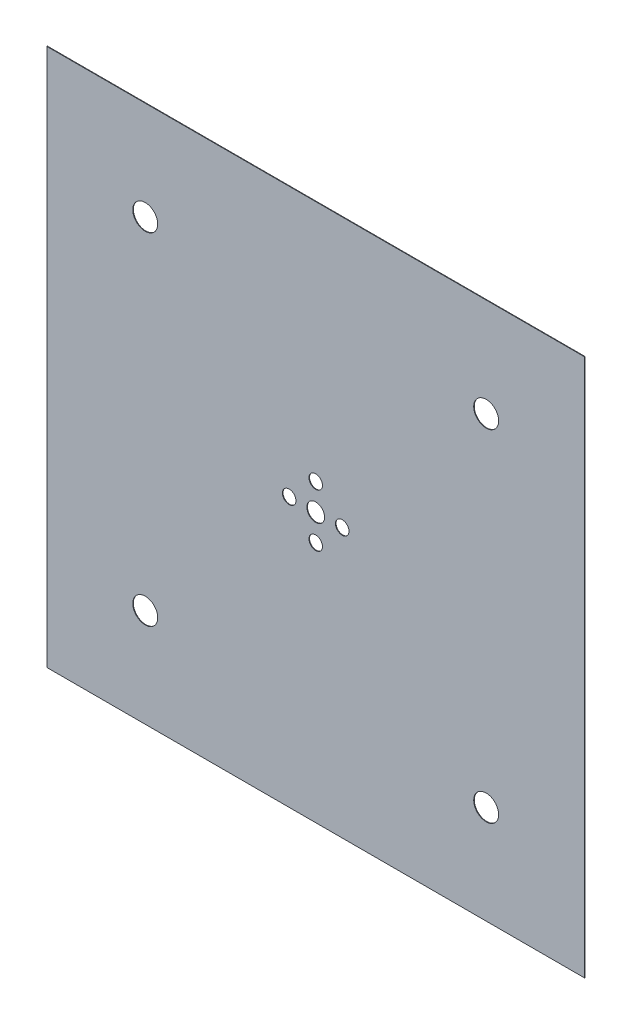
SolidWorks part; units mm, degrees
ref_plane "Front" through (0, 0, 0) normal (0, 0, 1) x (1, 0, 0)
ref_plane "Top" through (0, 0, 0) normal (0, 1, 0) x (1, 0, 0)
ref_plane "Right" through (0, 0, 0) normal (1, 0, 0) x (0, 0, -1)
sketch "Sketch1" plane through (0, 0, 0) normal (0, 0, 1) x (1, 0, 0)
  line L0 (0, 1420) -> (0, -1420) construction
  line L1 (-1420, 1420) -> (1420, 1420)
  line L2 (-1420, 1420) -> (-1420, -1420)
  line L3 (-1420, -1420) -> (1420, -1420)
  line L4 (1420, 1420) -> (1420, -1420)
  line L5 (-1420, 1420) -> (1420, -1420) construction
  line L6 (-1420, -1420) -> (1420, 1420) construction
  line L7 (-1420, 0) -> (1420, 0) construction
  circle A0 centre (0, 0) radius 46.75
  circle A1 centre (0, 140) radius 35.6375
  circle A2 centre (-900, 900) radius 65.8
  circle A3 centre (900, -900) radius 65.8
  circle A4 centre (0, -140) radius 35.6375
  circle A5 centre (900, 900) radius 65.8
  circle A6 centre (-900, -900) radius 65.8
  circle A7 centre (140, 0) radius 35.6375
  circle A8 centre (-140, 0) radius 35.6375
  point P0 (0, 0)
  dimension "D3" = 93.5
  dimension "D4" = 71.275
  dimension "D6" = 131.6
  dimension "D1" = 2840
  dimension "D2" = 2840
  dimension "D5" = 140
  dimension "D7" = 900
extrude "Boss-Extrude1" add sketch "Sketch1" along normal blind 3
